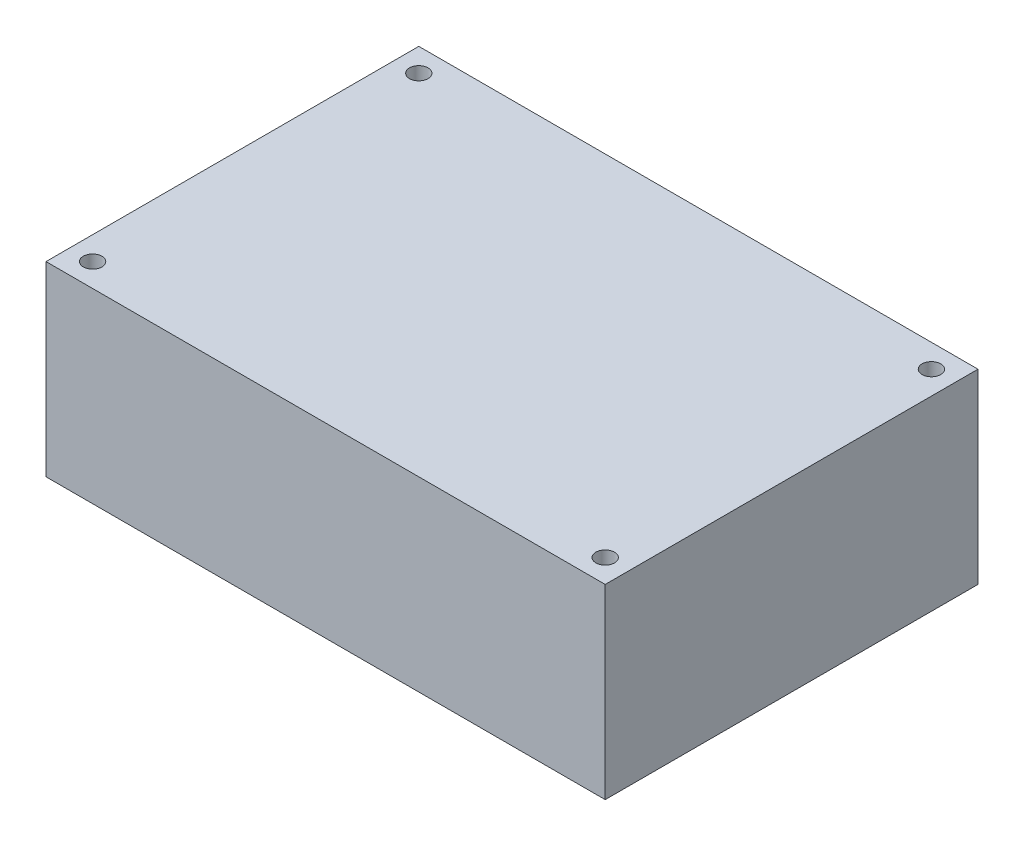
SolidWorks part; units mm, degrees
ref_plane "Front Plane" through (0, 0, 0) normal (0, 0, 1) x (1, 0, 0)
ref_plane "Top Plane" through (0, 0, 0) normal (0, 1, 0) x (1, 0, 0)
ref_plane "Right Plane" through (0, 0, 0) normal (1, 0, 0) x (0, 0, -1)
sketch "Sketch1" plane through (0, 0, 0) normal (0, 1, 0) x (1, 0, 0)
  line L1 (-30, 20) -> (30, 20)
  line L2 (-30, 20) -> (-30, -20)
  line L3 (-30, -20) -> (30, -20)
  line L4 (30, 20) -> (30, -20)
  line L5 (-30, 20) -> (30, -20) construction
  line L6 (-30, -20) -> (30, 20) construction
  line L7 (27.5, -17.5) -> (-27.5, -17.5) construction
  line L8 (27.5, -17.5) -> (27.5, 17.5) construction
  line L9 (27.5, 17.5) -> (-27.5, 17.5) construction
  line L10 (-27.5, -17.5) -> (-27.5, 17.5) construction
  line L11 (27.5, -17.5) -> (-27.5, 17.5) construction
  line L12 (27.5, 17.5) -> (-27.5, -17.5) construction
  circle A0 centre (-27.5, 17.5) radius 1
  circle A1 centre (27.5, 17.5) radius 1
  circle A2 centre (27.5, -17.5) radius 1
  circle A3 centre (-27.5, -17.5) radius 1
  point P0 (0, 0)
  point P5 (0, 0)
  dimension "D3" = 2
  dimension "D1" = 60
  dimension "D2" = 40
  dimension "D4" = 55
  dimension "D5" = 35
extrude "Boss-Extrude1" add sketch "Sketch1" along normal blind 20
